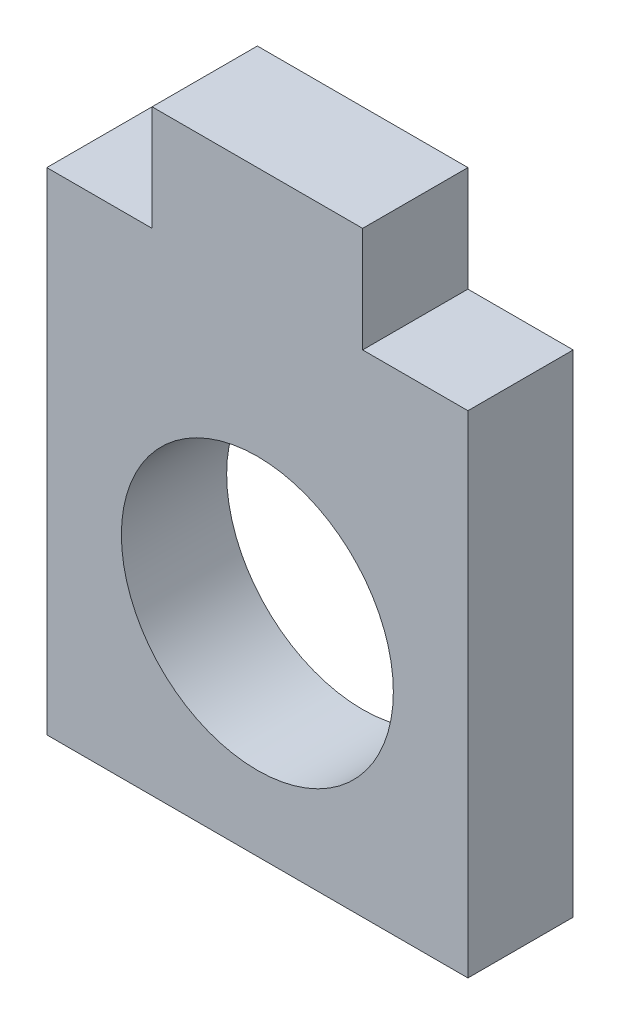
SolidWorks part; units mm, degrees
ref_plane "Front Plane" through (0, 0, 0) normal (0, 0, 1) x (1, 0, 0)
ref_plane "Top Plane" through (0, 0, 0) normal (0, 1, 0) x (1, 0, 0)
ref_plane "Right Plane" through (0, 0, 0) normal (1, 0, 0) x (0, 0, -1)
sketch "Sketch1" plane through (0, 0, 0) normal (0, 0, 1) x (1, 0, 0)
  line L1 (-6, 6) -> (6, 6)
  line L2 (-6, 6) -> (-6, -8)
  line L3 (-6, -8) -> (6, -8)
  line L4 (6, 6) -> (6, -8)
  point P0 (0, 0)
  dimension "D1" = 12
  dimension "D2" = 14
extrude "Boss-Extrude1" add sketch "Sketch1" along normal blind 3
sketch "Sketch2" plane through (0, 0, 3) normal (0, 0, 1) x (1, 0, 0)
  line L0 (6, 6) -> (-6, 6) construction
  circle A0 centre (0, -2) radius 3.875
  dimension "D1" = 7.75
  dimension "D2" = 8
extrude "Cut-Extrude1" cut sketch "Sketch2" against normal blind 3
sketch "Sketch3" plane through (0, 6, 0) normal (0, 1, 0) x (1, 0, 0)
  line L0 (6, 0) -> (-6, 0) construction
  line L1 (-3, 0) -> (3, 0)
  line L2 (-3, 0) -> (-3, -3)
  line L3 (-3, -3) -> (3, -3)
  line L4 (3, 0) -> (3, -3)
  line L5 (6, -3) -> (-6, -3) construction
  line L6 (-6, -3) -> (-6, 0) construction
  dimension "D1" = 6
  dimension "D2" = 3
extrude "Boss-Extrude2" add sketch "Sketch3" along normal blind 3
